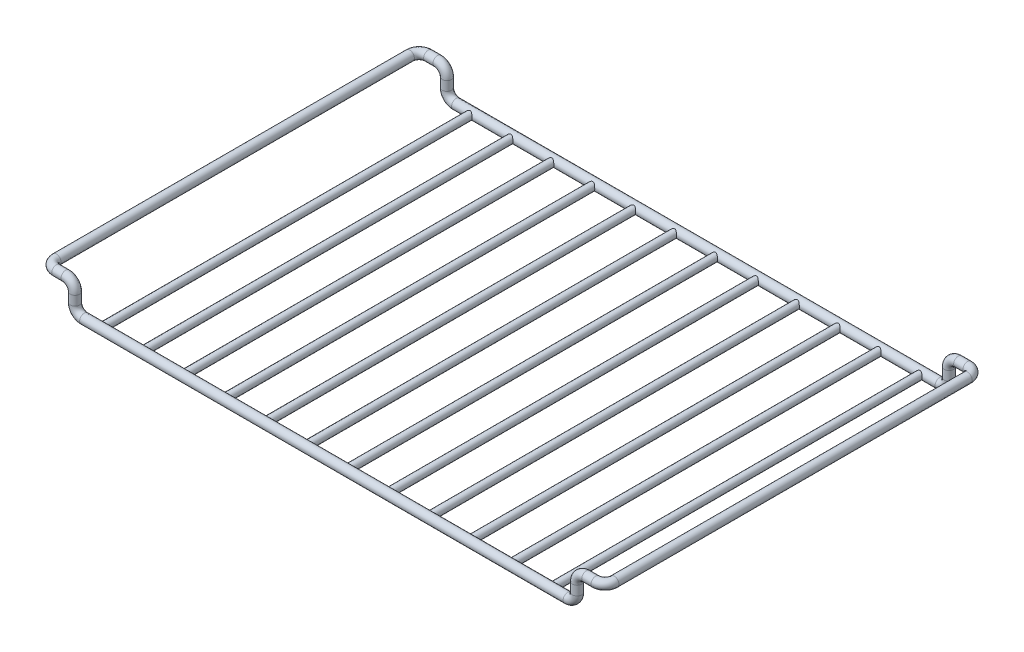
SolidWorks part; units mm, degrees
ref_plane "Alzado" through (0, 0, 0) normal (0, 0, 1) x (1, 0, 0)
ref_plane "Planta" through (0, 0, 0) normal (0, 1, 0) x (1, 0, 0)
ref_plane "Vista lateral" through (0, 0, 0) normal (1, 0, 0) x (0, 0, -1)
sketch3d "Croquis3D1"
  line L0 (0, 0, 0) -> (130, 0, 0)
  line L1 (135, 5, 0) -> (135, 10, 0)
  line L2 (140, 15, 0) -> (145, 15, 0)
  line L3 (150, 15, -5) -> (150, 15, -195)
  line L4 (145, 15, -200) -> (140, 15, -200)
  line L5 (135, 10, -200) -> (135, 5, -200)
  line L6 (130, 0, -200) -> (0, 0, -200)
  arc A0 (130, 0, 0) -> (135, 5, 0) centre (130, 5, 0) ccw
  arc A1 (135, 10, 0) -> (140, 15, 0) centre (140, 10, 0) ccw
  arc A2 (145, 15, 0) -> (150, 15, -5) centre (145, 15, -5) ccw
  arc A3 (150, 15, -195) -> (145, 15, -200) centre (145, 15, -195) ccw
  arc A4 (140, 15, -200) -> (135, 10, -200) centre (140, 10, -200) ccw
  arc A5 (135, 5, -200) -> (130, 0, -200) centre (130, 5, -200) ccw
  point P11 (135, 0, 0)
  point P12 (130, 5, 5)
  point P15 (135, 15, 0)
  point P16 (140, 10, -5)
  point P19 (150, 15, 0)
  point P20 (145, 20, -5)
  point P23 (150, 15, -200)
  point P24 (145, 20, -195)
  point P27 (135, 15, -200)
  point P28 (140, 10, -195)
  point P31 (135, 0, -200)
  point P32 (130, 5, -205)
  dimension "D8" = 5
  dimension "D9" = 5
  dimension "D10" = 5
  dimension "D11" = 5
  dimension "D12" = 5
  dimension "D13" = 5
  dimension "D1" = 135
  dimension "D2" = 200
  dimension "D3" = 15
  dimension "D4" = 15
  dimension "D5" = 15
  dimension "D6" = 15
  dimension "D7" = 135
sketch "Croquis1" plane through (0, 0, 0) normal (1, 0, 0) x (0, 0, -1)
  circle A0 centre (0, 0) radius 2.5
  dimension "D1" = 5
sweep "Barrer1" add profiles "Croquis1" path "Croquis3D1"
sketch "Croquis2" plane through (0, 0, 0) normal (0, 0, 1) x (1, 0, 0)
  line L0 (130, 0) -> (0, 0) construction
  circle A0 centre (11, 0) radius 2
  dimension "D1" = 4
  dimension "D2" = 11
extrude "Extruir1" add sketch "Croquis2" against normal up to surface (197.5 mm away) up to face at (130, 0, -197.5)
pattern_linear "MatrizL1" count 6 spacing 22 along (1, 0, 0) of "Extruir1"
mirror "Simetría1" about plane through (0, 0, 0) normal (1, 0, 0) of "MatrizL1", "Barrer1", "Extruir1"
